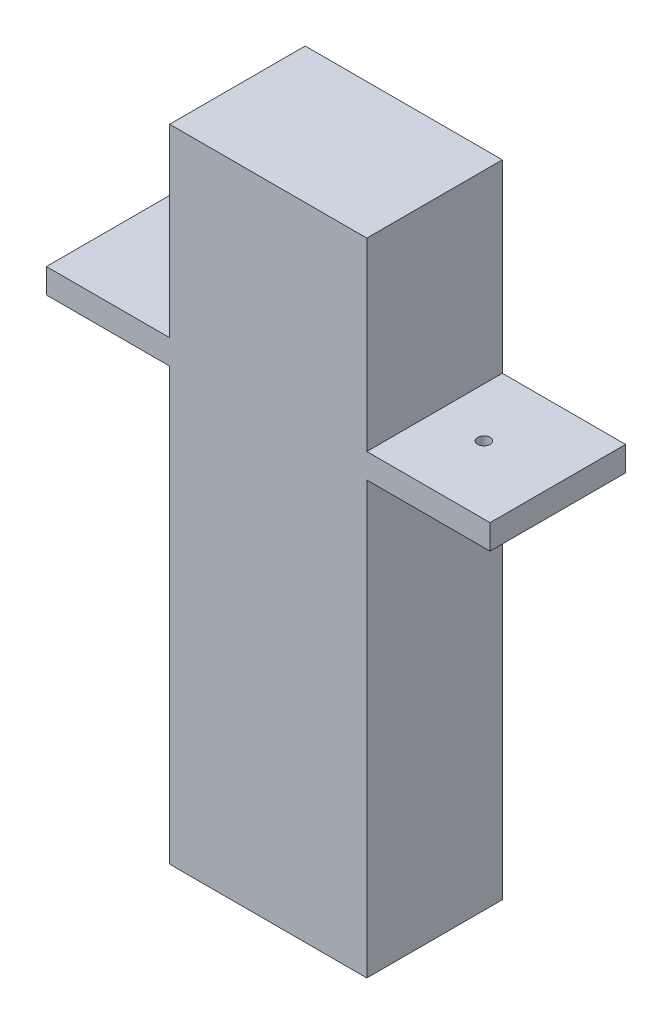
SolidWorks part; units mm, degrees
ref_plane "Plan de face" through (0, 0, 0) normal (0, 0, 1) x (1, 0, 0)
ref_plane "Plan de dessus" through (0, 0, 0) normal (0, 1, 0) x (1, 0, 0)
ref_plane "Plan de droite" through (0, 0, 0) normal (1, 0, 0) x (0, 0, -1)
sketch "Esquisse1" plane through (0, 0, 0) normal (0, 0, 1) x (1, 0, 0)
  line L1 (-6, 25) -> (6, 25)
  line L2 (-6, 25) -> (-6, -25)
  line L3 (-6, -25) -> (6, -25)
  line L4 (6, 25) -> (6, -25)
  line L5 (-6, 25) -> (6, -25) construction
  line L6 (-6, -25) -> (6, 25) construction
  line L7 (-8, -25) -> (8, -25)
  line L8 (-8, -25) -> (-8, 27)
  line L9 (-8, 27) -> (8, 27)
  line L10 (8, -25) -> (8, 27)
  point P0 (0, 0)
  dimension "D1" = 50
  dimension "D2" = 12
  dimension "D3" = 2
  dimension "D4" = 2
  dimension "D5" = 2
extrude "Boss.-Extru.1" add sketch "Esquisse1" along normal blind 9 contours L7 L10 L9 L8 L2 L1 L4
sketch "Esquisse2" plane through (0, 0, 9) normal (0, 0, 1) x (1, 0, 0)
  line L1 (-8, 27) -> (8, 27)
  line L2 (-8, 27) -> (-8, -25)
  line L3 (-8, -25) -> (8, -25)
  line L4 (8, 27) -> (8, -25)
extrude "Boss.-Extru.2" add sketch "Esquisse2" along normal blind 2
sketch "Esquisse5" plane through (0, 0, 9) normal (0, 0, -1) x (-1, 0, 0)
  line L0 (6, 25) -> (-6, 25) construction
  circle A0 centre (0, 4) radius 1.75
  dimension "D1" = 21
  dimension "D2" = 3.5
extrude "Boss.-Extru.5" add sketch "Esquisse5" along normal blind 5
sketch "Esquisse6" plane through (0, 0, 4) normal (0, 0, -1) x (-1, 0, 0)
  circle A0 centre (0, 4) radius 0.5
  dimension "D1" = 1
extrude "Enlèv. mat.-Extru.1" cut sketch "Esquisse6" against normal blind 5
sketch "Esquisse11" plane through (-8, 0, 0) normal (-1, 0, 0) x (0, 0, 1)
  line L0 (0, -25) -> (0, 27) construction
  line L1 (0, 12) -> (11, 12)
  line L2 (0, 12) -> (0, 10)
  line L3 (0, 10) -> (11, 10)
  line L4 (11, 12) -> (11, 10)
  line L5 (11, 27) -> (11, -25) construction
  line L6 (11, 27) -> (0, 27) construction
  dimension "D1" = 15
  dimension "D2" = 2
  dimension "D3" = 11
extrude "Boss.-Extru.6" add sketch "Esquisse11" along normal blind 10
sketch "Esquisse12" plane through (0, 12, 0) normal (0, 1, 0) x (1, 0, 0)
  line L0 (-8, -11) -> (-8, 0) construction
  line L1 (-18, -11) -> (-8, -11) construction
  circle A0 centre (-12, -5.5) radius 0.5
  dimension "D1" = 4
  dimension "D3" = 1
  dimension "D2" = 5.5
extrude "Enlèv. mat.-Extru.2" cut sketch "Esquisse12" against normal through all
mirror "Symétrie1" about plane through (0, 0, 0) normal (1, 0, 0) of "Enlèv. mat.-Extru.2", "Boss.-Extru.6"
